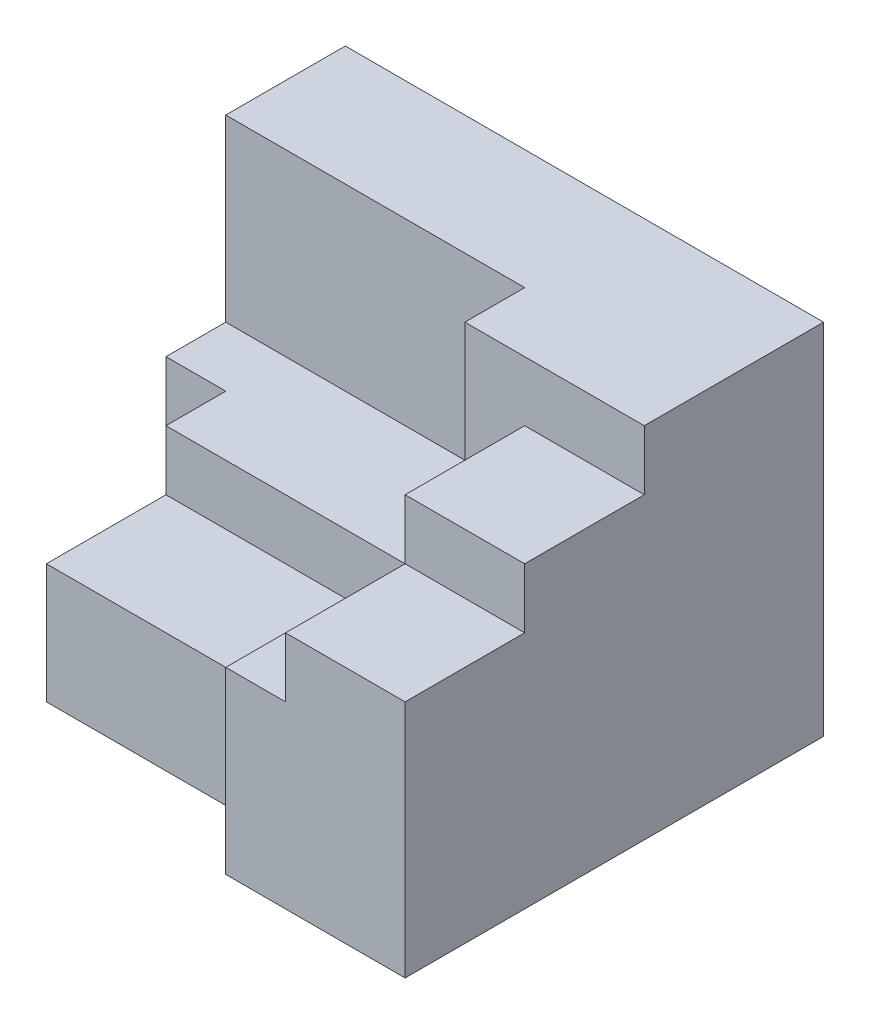
SolidWorks part; units mm, degrees
ref_plane "Front Plane" through (0, 0, 0) normal (0, 0, 1) x (1, 0, 0)
ref_plane "Top Plane" through (0, 0, 0) normal (0, 1, 0) x (1, 0, 0)
ref_plane "Right Plane" through (0, 0, 0) normal (1, 0, 0) x (0, 0, -1)
sketch "Sketch1" plane through (0, 0, 0) normal (0, 1, 0) x (1, 0, 0)
  line L1 (-4, -3.5) -> (4, -3.5)
  line L2 (-4, -3.5) -> (-4, 3.5)
  line L3 (-4, 3.5) -> (4, 3.5)
  line L4 (4, -3.5) -> (4, 3.5)
  line L5 (-4, -3.5) -> (4, 3.5) construction
  line L6 (-4, 3.5) -> (4, -3.5) construction
  point P0 (0, 0)
  dimension "D1" = 7
  dimension "D2" = 8
extrude "Boss-Extrude1" add sketch "Sketch1" along normal blind 6
sketch "Sketch2" plane through (0, 6, 0) normal (0, 1, 0) x (1, 0, 0)
  line L0 (-4, 0.5) -> (-3, 0.5)
  line L1 (-4, 3.5) -> (-4, -3.5) construction
  line L2 (-3, 0.5) -> (-3, -2.5)
  line L3 (-3, -2.5) -> (1, -2.5)
  line L4 (1, -2.5) -> (1, -3.5)
  line L5 (-4, -3.5) -> (4, -3.5) construction
  line L6 (1, -3.5) -> (-4, -3.5)
  line L7 (-4, -3.5) -> (-4, 0.5)
  dimension "D1" = 3
  dimension "D2" = 4
  dimension "D3" = 1
  dimension "D4" = 1
extrude "Cut-Extrude1" cut sketch "Sketch2" against normal blind 60
sketch "Sketch4" plane through (0, 6, 0) normal (0, 1, 0) x (1, 0, 0)
  line L0 (-4, 1.5) -> (1, 1.5)
  line L1 (-4, 3.5) -> (-4, 0.5) construction
  line L2 (1, 1.5) -> (1, 0.5)
  line L3 (1, 0.5) -> (2, 0.5)
  line L4 (2, 0.5) -> (2, -4.4559)
  line L5 (2, -4.4559) -> (-4, -3.6895)
  line L6 (-4, -3.6895) -> (-4, 1.5)
  line L7 (4, -3.5) -> (4, 3.5) construction
  line L8 (4, 3.5) -> (-4, 3.5) construction
  dimension "D1" = 1
  dimension "D2" = 1
  dimension "D3" = 2
  dimension "D4" = 2
extrude "Cut-Extrude2" cut sketch "Sketch4" against normal blind 3
sketch "Sketch5" plane through (0, 3, 0) normal (0, 1, 0) x (1, 0, 0)
  line L1 (-3, -2.5) -> (1, -2.5)
  line L2 (-3, -2.5) -> (-3, -0.5)
  line L3 (-3, -0.5) -> (1, -0.5)
  line L4 (1, -2.5) -> (1, -0.5)
  dimension "D1" = 2
  dimension "D2" = 4
extrude "Cut-Extrude3" cut sketch "Sketch5" against normal blind 1
sketch "Sketch6" plane through (0, 6, 0) normal (0, 1, 0) x (1, 0, 0)
  line L1 (2, 0.5) -> (5.0011, 0.5)
  line L2 (2, 0.5) -> (2, -4.361)
  line L3 (2, -4.361) -> (5.0011, -4.361)
  line L4 (5.0011, 0.5) -> (5.0011, -4.361)
extrude "Cut-Extrude4" cut sketch "Sketch6" against normal blind 1
sketch "Sketch7" plane through (0, 5, 0) normal (0, 1, 0) x (1, 0, 0)
  line L0 (4, -3.5) -> (4, 0.5) construction
  line L1 (2, -3.5) -> (4, -3.5)
  line L2 (2, -3.5) -> (2, -1.5)
  line L3 (2, -1.5) -> (4, -1.5)
  line L4 (4, -3.5) -> (4, -1.5)
  dimension "D1" = 2
extrude "Cut-Extrude5" cut sketch "Sketch7" against normal blind 1
